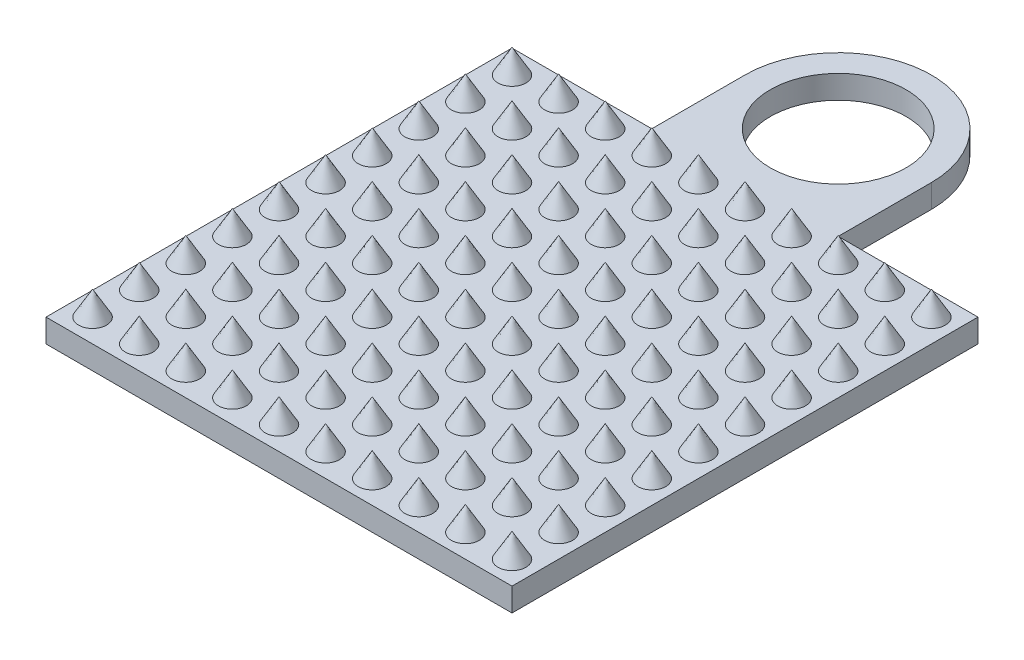
SolidWorks part; units mm, degrees
ref_plane "Front Plane" through (0, 0, 0) normal (0, 0, 1) x (1, 0, 0)
ref_plane "Top Plane" through (0, 0, 0) normal (0, 1, 0) x (1, 0, 0)
ref_plane "Right Plane" through (0, 0, 0) normal (1, 0, 0) x (0, 0, -1)
sketch "Sketch1" plane through (0, 0, 0) normal (0, 1, 0) x (1, 0, 0)
  line L1 (5, -5) -> (-5, -5)
  line L2 (5, -5) -> (5, 5)
  line L3 (5, 5) -> (-5, 5)
  line L4 (-5, -5) -> (-5, 5)
  line L5 (5, -5) -> (-5, 5) construction
  line L6 (5, 5) -> (-5, -5) construction
  point P0 (0, 0)
  dimension "D1" = 10
  dimension "D2" = 10
extrude "Plate" add sketch "Sketch1" along normal blind 0.5
sketch "Sketch2" plane through (0, 0.5, 0) normal (0, 1, 0) x (1, 0, 0)
  line L0 (-5, -5) -> (5, -5) construction
  line L1 (-5, 5) -> (-5, -5) construction
  circle A0 centre (-4.5, -4.5) radius 0.3
  dimension "D1" = 0.6
  dimension "D2" = 0.5
  dimension "D3" = 0.5
sketch "Sketch4" plane through (0, 0, 0) normal (0, 1, 0) x (1, 0, 0)
  line L5 (-2, 7) -> (-2, 5)
  line L6 (5, 5) -> (-5, 5) construction
  line L8 (-5, 5) -> (-5, -5) construction
  line L9 (-2, 5) -> (2, 5)
  line L10 (2, 5) -> (2, 7)
  arc A0 (-2, 7) -> (2, 7) centre (0, 7) cw
  point P0 (0, 7)
  dimension "D3" = 5
extrude "Boss-Extrude3" add sketch "Sketch4" along normal blind 0.5
sketch "Sketch5" plane through (0, 0.5, 0) normal (0, 1, 0) x (1, 0, 0)
  circle A0 centre (0, 7) radius 1.4559
extrude "Cut-Extrude1" cut sketch "Sketch5" against normal blind 1.5 and the other way blind 0.5
extrude "Cone" add sketch "Sketch2" along normal blind 10.25 draft 30
pattern_linear "LPattern1" count 10 spacing 1 along (1, 0, 0) count 10 spacing 1 along (0, 0, -1) of "Cone"
